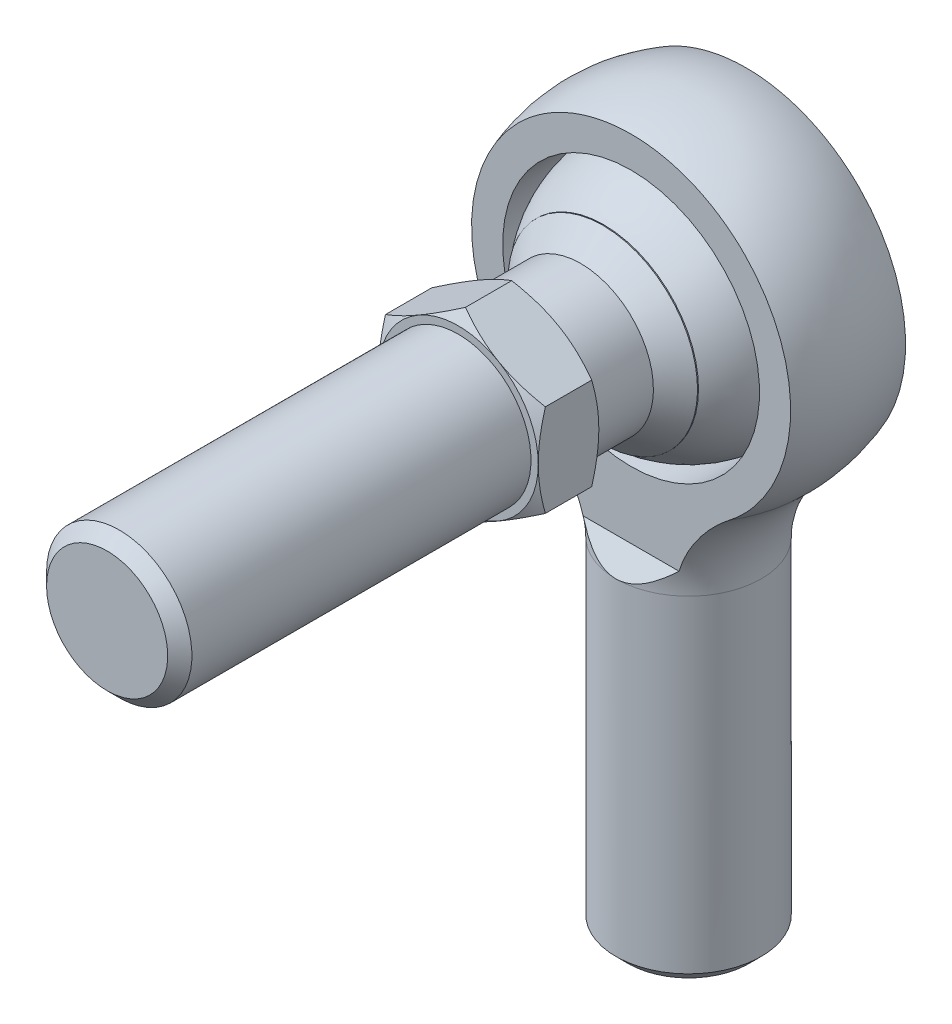
SolidWorks part; units mm, degrees
ref_plane "Front" through (0, 0, 0) normal (0, 0, 1) x (1, 0, 0)
ref_plane "Top" through (0, 0, 0) normal (0, 1, 0) x (1, 0, 0)
ref_plane "Right" through (0, 0, 0) normal (1, 0, 0) x (0, 0, -1)
sketch "Sketch1" plane through (0, 0, 0) normal (0, 0, 1) x (1, 0, 0)
  line L0 (0, 0) -> (0, -44.45)
  line L1 (0, -44.45) -> (9.525, -44.45)
  line L2 (9.525, -44.45) -> (9.525, 0)
  line L3 (9.525, 0) -> (0, 0)
  line L5 (0, 50.8) -> (0, 0) construction
  line L6 (0, 50.8) -> (22.225, 50.8) construction
  line L7 (22.225, 50.8) -> (22.225, 28.575) construction
  line L8 (-9.525, -44.45) -> (-9.525, 0) construction
  arc A0 (14.893, 12.0781) -> (0, 50.8) centre (0, 28.575) ccw construction
  circle A1 centre (0, 28.575) radius 9.525 construction
  circle A2 centre (0, 28.575) radius 16.6624 construction
  circle A3 centre (0, 28.575) radius 16.829 construction
  arc A4 (9.525, 0) -> (14.893, 12.0781) centre (25.7969, 0) cw construction
  dimension "D1" = 33.658
  dimension "A" = 19.05
  dimension "Ball Dia" = 33.3248
  dimension "B" = 44.45
  dimension "D" = 73.025
  dimension "E" = 44.45
  dimension "Thread Dia" = 19.05
revolve "Revolve1" add sketch "Sketch1" angle 360 about L5
chamfer "Chamfer2" distance 1.5875 angle 45 1 edges at (-9.525, -44.45, 0)
sketch "Sketch21" plane through (0, -44.45, 0) normal (0, -1, 0) x (1, 0, 0)
  circle A1 centre (0, 0) radius 7.9375
  circle A2 centre (0, 0) radius 7.9375
  dimension "D1" = 0
sketch "Sketch22" plane through (0, 0, 0) normal (0, 0, 1) x (1, 0, 0)
  line L0 (9.525, -44.45) -> (9.525, -45.8391)
  line L1 (9.525, -45.8391) -> (8.4939, -45.2437)
  line L2 (8.4939, -45.2437) -> (8.4939, -45.0453)
  line L3 (8.4939, -45.0453) -> (9.525, -44.45)
  line L4 (9.0094, -44.7477) -> (9.0094, -45.5414) construction
  dimension "D1" = 60
  dimension "D2" = 0.7937
  dimension "D3" = 0.1984
sketch "Sketch4" plane through (0, 0, 0) normal (0, 0, 1) x (1, 0, 0)
  line L0 (9.525, 0) -> (0, 0) construction
  line L2 (0, 50.8) -> (0, 0) construction
  line L3 (9.525, 0) -> (0, 0)
  line L5 (0, 50.8) -> (0, 0)
  line L6 (0, 50.8) -> (0, 53.34) construction
  arc A0 (14.893, 12.0781) -> (0, 50.8) centre (0, 28.575) ccw construction
  arc A1 (14.893, 12.0781) -> (0, 50.8) centre (0, 28.575) ccw
  arc A2 (14.893, 12.0781) -> (9.525, 0) centre (25.7969, 0) ccw construction
  arc A3 (14.893, 12.0781) -> (9.525, 0) centre (25.7969, 0) ccw
  dimension "D1" = 2.54
revolve "Revolve2" add sketch "Sketch4" angle 360 about L6
sketch "Sketch5" plane through (0, 0, 0) normal (1, 0, 0) x (0, 0, -1)
  line L0 (7.5311, 50.8) -> (22.225, 50.8)
  line L1 (-7.5311, 50.8) -> (7.5311, 50.8) construction
  line L2 (-7.5311, 50.8) -> (-7.5311, 3.0124)
  line L3 (-9.525, 0) -> (9.525, 0) construction
  line L4 (7.5311, 50.8) -> (7.5311, 3.0124)
  line L5 (22.225, 50.8) -> (22.225, 0)
  line L6 (22.225, 0) -> (9.525, 0)
  line L7 (-9.525, 0) -> (-22.225, 0)
  line L8 (-22.225, 0) -> (-22.225, 50.8)
  line L9 (-22.225, 50.8) -> (-7.5311, 50.8)
  line L10 (9.525, 0) -> (7.5311, 3.0124)
  line L11 (-9.525, 0) -> (-7.5311, 3.0124)
  line L12 (-7.5311, 3.0124) -> (7.5311, 3.0124) construction
  line L13 (0, 0) -> (0, 3.0124) construction
  arc A0 (14.893, 12.0781) -> (-14.893, 12.0781) centre (0, 28.575) ccw construction
  dimension "D1" = 19.05
  dimension "F" = 15.0622
  dimension "D2" = 3.0124
extrude "Cut-Extrude1" cut sketch "Sketch5" against normal through all and the other way through all
sketch "Sketch6" plane through (0, 0, 0) normal (0, 0, 1) x (1, 0, 0)
  circle A0 centre (0, 28.575) radius 16.829 construction
  circle A1 centre (0, 28.575) radius 16.829
extrude "Cut-Extrude2" cut sketch "Sketch6" against normal through all and the other way through all
sketch "Sketch7" plane through (0, 0, 0) normal (0, 0, 1) x (1, 0, 0)
  line L0 (0, 45.2374) -> (0, 11.9126)
  line L1 (0, 50.8) -> (0, 0) construction
  line L2 (0, 0) -> (0, 11.9126) construction
  arc A0 (0, 11.9126) -> (0, 45.2374) centre (0, 28.575) ccw
  circle A1 centre (0, 28.575) radius 16.6624 construction
revolve "Revolve3" add sketch "Sketch7" angle 360 about L2
sketch "Sketch8" plane through (0, 0, 0) normal (1, 0, 0) x (0, 0, -1)
  line L0 (-7.5311, 50.8) -> (7.5311, 50.8) construction
  line L1 (-11.1125, 50.8) -> (11.1125, 50.8) construction
  line L2 (-11.1125, 50.8) -> (-11.1125, 0)
  line L3 (-11.1125, 0) -> (11.1125, 0) construction
  line L4 (11.1125, 50.8) -> (11.1125, 0)
  line L5 (11.1125, 50.8) -> (22.225, 50.8)
  line L6 (22.225, 50.8) -> (22.225, 0)
  line L7 (22.225, 0) -> (11.1125, 0)
  line L8 (-11.1125, 0) -> (-22.225, 0)
  line L9 (-22.225, 0) -> (-22.225, 50.8)
  line L10 (-22.225, 50.8) -> (-11.1125, 50.8)
  dimension "C" = 22.225
extrude "Cut-Extrude3" cut sketch "Sketch8" against normal through all and the other way through all
sketch "Sketch10" plane through (0, 0, 0) normal (0, 0, 1) x (1, 0, 0)
  circle A0 centre (0, 28.575) radius 9.525 construction
  circle A1 centre (0, 28.575) radius 9.525
extrude "Cut-Extrude4" cut sketch "Sketch10" against normal through all and the other way through all
chamfer "Chamfer1" distance 0.9525 angle 45 2 edges at (9.525, 28.575, -11.1125) (9.525, 28.575, 11.1125)
sketch "Sketch12" plane through (0, 0, 0) normal (1, 0, 0) x (0, 0, -1)
  line L1 (11.1125, 28.575) -> (-76.2, 28.575) construction
  line L2 (11.1125, 28.575) -> (11.1125, 38.1) construction
  line L3 (-34.925, 38.1) -> (11.1125, 38.1) construction
  line L4 (-76.2, 28.575) -> (-76.2, 38.1)
  line L5 (11.1125, 16.1594) -> (11.1125, 40.9906) construction
  line L6 (11.1125, 28.575) -> (20.6375, 28.575) construction
  line L14 (0, 38.1) -> (0, 28.575) construction
  line L15 (0, 50.8) -> (0, 0) construction
  line L20 (11.1125, 19.05) -> (-76.2, 19.05) construction
  line L21 (-34.925, 38.1) -> (-34.925, 19.05) construction
  line L22 (-30.1752, 38.1) -> (-30.1752, 19.05) construction
  line L23 (-34.925, 38.1) -> (-34.925, 28.575)
  line L24 (-34.925, 38.1) -> (-76.2, 38.1)
  line L25 (-34.925, 28.575) -> (-76.2, 28.575)
  dimension "L Length" = 76.2
  dimension "S Thread Length" = 41.275
  dimension "P Length" = 46.0248
revolve "Revolve4" add sketch "Sketch12" angle 360 about L6
chamfer "Chamfer3" distance 1.5875 angle 45 1 edges at (9.525, 28.575, 76.2)
sketch "Sketch23" plane through (0, 0, 34.925) normal (0, 0, -1) x (-1, 0, 0)
  circle A1 centre (0, 28.575) radius 9.525
  circle A2 centre (0, 28.575) radius 9.525
  dimension "D1" = 0
sketch "Sketch24" plane through (0, 0, 0) normal (1, 0, 0) x (0, 0, -1)
  line L0 (-34.925, 38.1) -> (-33.5359, 38.1)
  line L1 (-33.5359, 38.1) -> (-34.1313, 37.0689)
  line L2 (-34.1313, 37.0689) -> (-34.3297, 37.0689)
  line L3 (-34.3297, 37.0689) -> (-34.925, 38.1)
  line L4 (-34.6273, 37.5844) -> (-33.8336, 37.5844) construction
  dimension "D1" = 60
  dimension "D2" = 0.7937
  dimension "D3" = 0.1984
sketch "Sketch15" plane through (0, 0, 0) normal (1, 0, 0) x (0, 0, -1)
  line L0 (11.1125, 28.575) -> (20.6375, 28.575) construction
  line L1 (-34.925, 28.575) -> (11.1125, 28.575)
  line L2 (-34.925, 28.575) -> (-34.925, 38.1)
  line L3 (-34.925, 38.1) -> (11.1125, 38.1)
  line L4 (11.1125, 28.575) -> (11.1125, 38.1)
  line L5 (11.1125, 28.575) -> (20.6375, 28.575) construction
revolve "Revolve5" add sketch "Sketch15" angle 360 about L5
ref_plane "Plane1" through (0, 0, 30.1752) normal (0, 0, 1) x (1, 0, 0)
sketch "Sketch16" plane through (0, 0, 30.1752) normal (0, 0, 1) x (1, 0, 0)
  line L1 (0, 40.6734) -> (-10.4775, 34.6242)
  line L2 (-10.4775, 34.6242) -> (-10.4775, 22.5258)
  line L3 (-10.4775, 22.5258) -> (0, 16.4766)
  line L4 (0, 16.4766) -> (10.4775, 22.5258)
  line L5 (10.4775, 22.5258) -> (10.4775, 34.6242)
  line L6 (10.4775, 34.6242) -> (0, 40.6734)
  circle A0 centre (0, 28.575) radius 10.4775 construction
  dimension "D1" = 20.955
extrude "Extrude1" add sketch "Sketch16" against normal blind 7.9375
sketch "Sketch17" plane through (0, 0, 30.1752) normal (0, 0, 1) x (1, 0, 0)
  circle A0 centre (0, 28.575) radius 10.4775 construction
  circle A1 centre (0, 28.575) radius 10.4775
extrude "Cut-Extrude5" cut sketch "Sketch17" against normal through all draft 60 flip side to cut
sketch "Sketch18" plane through (0, 0, 22.2377) normal (0, 0, -1) x (-1, 0, 0)
  circle A0 centre (0, 28.575) radius 10.4775 construction
  circle A1 centre (0, 28.575) radius 10.4775
extrude "Cut-Extrude6" cut sketch "Sketch18" against normal through all draft 60 flip side to cut
sketch "Sketch20" plane through (0, 0, 0) normal (1, 0, 0) x (0, 0, -1)
  line L0 (-11.2395, 40.9906) -> (-14.1301, 38.1)
  line L1 (-14.1301, 38.1) -> (-11.2395, 38.1)
  line L2 (-11.2395, 38.1) -> (-11.2395, 40.9906)
  line L3 (-34.925, 38.1) -> (11.1125, 38.1) construction
  line L4 (-11.1125, 40.9906) -> (-11.2395, 40.9906) construction
  line L6 (-11.1125, 40.9906) -> (-11.1125, 16.1594) construction
  line L7 (11.1125, 28.575) -> (-76.2, 28.575) construction
  line L8 (11.1125, 28.575) -> (-76.2, 28.575) construction
  arc A0 (11.1125, 40.9906) -> (-11.1125, 40.9906) centre (0, 28.575) ccw construction
  dimension "D1" = 0.127
  dimension "D2" = 45
revolve "Revolve6" add sketch "Sketch20" angle 360 about L8
sketch "Sketch11" plane through (0, 0, 0) normal (1, 0, 0) x (0, 0, -1)
  line L0 (0, 28.575) -> (-11.1125, 33.292) construction
  line L1 (7.5311, 28.575) -> (-7.5311, 28.575) construction
  line L2 (0, 28.575) -> (-11.1125, 23.858) construction
  line L3 (0, 50.8) -> (0, 0) construction
  line L4 (-11.1125, 50.8) -> (-11.1125, 0) construction
  line L5 (0, 28.575) -> (0.4676, 28.7735) construction
  line L7 (0.4676, 28.3765) -> (0, 28.575) construction
  dimension "D1" = 0.508
  dimension "Swivel" = 46
equation "\"D1@Sketch1\"=\"Ball Dia@Sketch1\"*1.01"
equation "\"D1@Chamfer1\"=\"A@Sketch1\"/20"
equation "\"D1@Sketch5\"=\"Thread Dia@Sketch1\""
equation "\"D2@Sketch5\"=\"F@Sketch5\"/5"
equation "\"D1@Sketch16\"=\"A@Sketch1\"*1.1"
equation "\"D1@Extrude1\"= \"D4@Helix/Spiral3\" * 5"
equation "\"D3@Helix/Spiral1\" = \"E@Sketch1\" + .125"
equation "\"D3@Sketch22\" = \"D4@Helix/Spiral1\" * .125"
equation "\"D2@Sketch22\" = \"D4@Helix/Spiral1\" * .5"
equation "\"D1@Chamfer2\" = \"D4@Helix/Spiral1\" * 1"
equation "\"D3@Helix/Spiral3\" = \"S Thread Length@Sketch12\" + .2"
equation "\"D3@Sketch24\" = \"D4@Helix/Spiral3\" * .125"
equation "\"D2@Sketch24\" = \"D4@Helix/Spiral3\" * .5"
equation "\"D1@Chamfer3\" = \"D4@Helix/Spiral3\" * 1"
